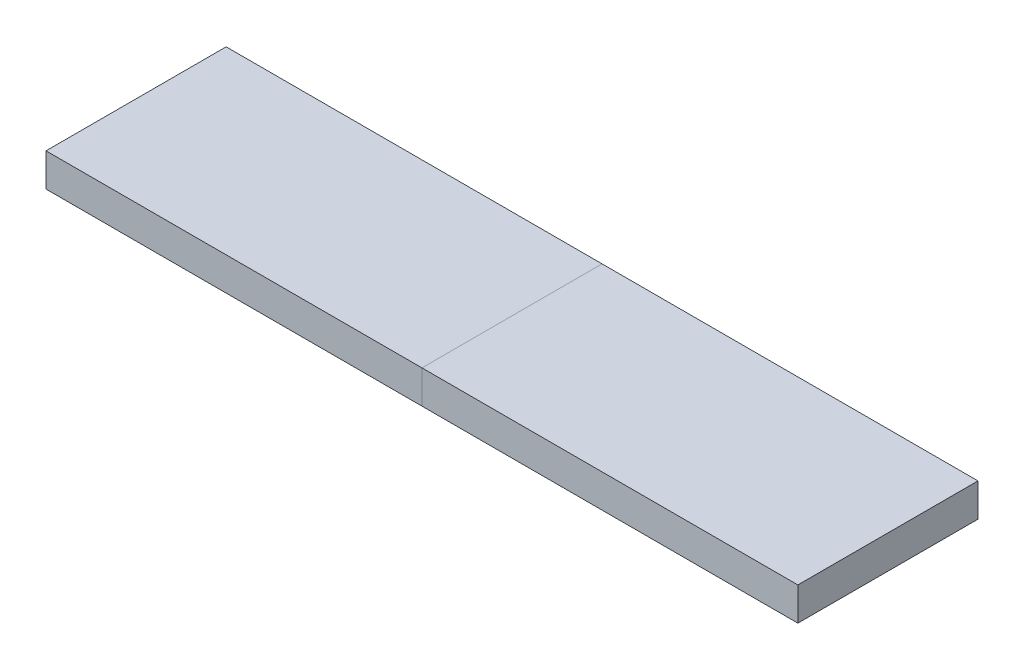
SolidWorks part; units mm, degrees
ref_plane "Front Plane" through (0, 0, 0) normal (0, 0, 1) x (1, 0, 0)
ref_plane "Top Plane" through (0, 0, 0) normal (0, 1, 0) x (1, 0, 0)
ref_plane "Right Plane" through (0, 0, 0) normal (1, 0, 0) x (0, 0, -1)
sketch "Sketch2" plane through (0, 0, 0) normal (0, 1, 0) x (1, 0, 0)
  line L1 (-144, 34.5) -> (144, 34.5)
  line L2 (-144, 34.5) -> (-144, -34.5)
  line L3 (-144, -34.5) -> (144, -34.5)
  line L4 (144, 34.5) -> (144, -34.5)
  line L5 (-144, 34.5) -> (144, -34.5) construction
  line L6 (-144, -34.5) -> (144, 34.5) construction
  point P0 (0, 0)
  dimension "D1" = 69
  dimension "D2" = 288
extrude "Boss-Extrude1" add sketch "Sketch2" along normal mid plane 12.7
sketch "Sketch3" plane through (0, -6.35, 0) normal (0, -1, 0) x (1, 0, 0)
  line L1 (-140.0969, -30.9562) -> (140.0969, -30.9562)
  line L2 (-140.0969, -30.9562) -> (-140.0969, 30.9562)
  line L3 (-140.0969, 30.9562) -> (140.0969, 30.9562)
  line L4 (140.0969, -30.9562) -> (140.0969, 30.9562)
  line L5 (-140.0969, -30.9562) -> (140.0969, 30.9562) construction
  line L6 (-140.0969, 30.9562) -> (140.0969, -30.9562) construction
  point P0 (0, 0)
  dimension "D1" = 280.1938
  dimension "D2" = 61.9125
extrude "Cut-Extrude1" cut sketch "Sketch3" against normal blind 6.35
sketch "Sketch4" plane through (0, 0, 0) normal (0, -1, 0) x (1, 0, 0)
  line L1 (-135.675, 27.5) -> (135.675, 27.5)
  line L2 (-135.675, 27.5) -> (-135.675, -27.5)
  line L3 (-135.675, -27.5) -> (135.675, -27.5)
  line L4 (135.675, 27.5) -> (135.675, -27.5)
  line L5 (-135.675, 27.5) -> (135.675, -27.5) construction
  line L6 (-135.675, -27.5) -> (135.675, 27.5) construction
  point P0 (0, 0)
  dimension "D1" = 271.35
  dimension "D2" = 55
extrude "Cut-Extrude2" cut sketch "Sketch4" against normal blind 4
sketch "Sketch5" plane through (0, 6.35, 0) normal (0, 1, 0) x (1, 0, 0)
  line L0 (0, -34.5) -> (0, 34.5)
  line L1 (-144, -34.5) -> (144, -34.5) construction
  line L2 (144, 34.5) -> (-144, 34.5) construction
split "Split1" trim tools "Sketch5" bodies to split 103 resulting bodies 106 107
